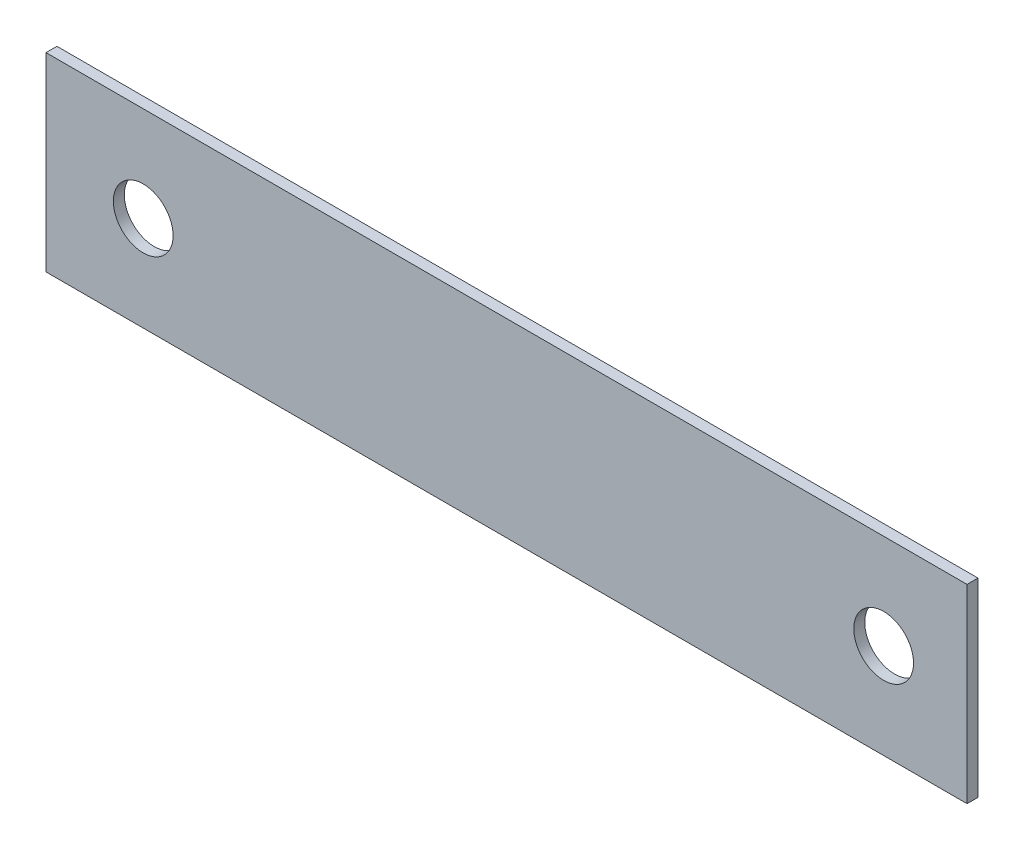
SolidWorks part; units mm, degrees
ref_plane "Front Plane" through (0, 0, 0) normal (0, 0, 1) x (1, 0, 0)
ref_plane "Top Plane" through (0, 0, 0) normal (0, 1, 0) x (1, 0, 0)
ref_plane "Right Plane" through (0, 0, 0) normal (1, 0, 0) x (0, 0, -1)
sketch "Sketch1" plane through (0, 0, 0) normal (0, 0, 1) x (1, 0, 0)
  line L1 (-18.5, -3.815) -> (18.5, -3.815)
  line L2 (-18.5, -3.815) -> (-18.5, 3.815)
  line L3 (-18.5, 3.815) -> (18.5, 3.815)
  line L4 (18.5, -3.815) -> (18.5, 3.815)
  line L5 (-18.5, -3.815) -> (18.5, 3.815) construction
  line L6 (-18.5, 3.815) -> (18.5, -3.815) construction
  circle A0 centre (-14.5941, 0) radius 1.2
  circle A1 centre (15.15, 0) radius 1.2
  point P0 (0, 0)
  point P10 (0, 0)
  point P11 (0, 0)
  dimension "D3" = 2.4
  dimension "D4" = 2.4
  dimension "D1" = 37
  dimension "D2" = 7.63
  dimension "D5" = 3.35
  dimension "D6" = 3.9059
extrude "Boss-Extrude1" add sketch "Sketch1" along normal blind 0.44
ref_plane "Plane1" through (-5.295, 0, 0) normal (1, 0, 0) x (0, 0, -1)
sketch "Sketch3" plane through (-5.295, 0, 0) normal (1, 0, 0) x (0, 0, -1)
  line L0 (2.2275, 0.8907) -> (0, 2.71)
  line L2 (2.2275, -0.8907) -> (0, -2.71)
  line L3 (0, 2.71) -> (0, -2.71)
  arc A0 (2.2275, -0.8907) -> (2.2275, 0.8907) centre (1.5, 0) ccw
  circle A1 centre (1.5, 0) radius 1.05
  point P6 (0, 0)
  point P7 (1.5555, 0)
  point P10 (1.3723, 1.15)
  point P11 (1.0898, -1.6004)
  point P12 (1.4792, 0)
  point P13 (0, 0)
  point P14 (2.196, 0.9154)
  point P15 (2.1244, -0.9657)
  dimension "D1" = 2.3
  dimension "D2" = 2.1
  dimension "D3" = 5.42
  dimension "D4" = 1.5
sketch "Sketch4" plane through (0, 0, 0) normal (0, 1, 0) x (1, 0, 0)
  line L0 (-5.295, 1.5) -> (-5.295, 0) construction
  line L1 (18.5, 0) -> (-18.5, 0) construction
  arc A0 (-5.295, 1.5) -> (-7.6188, 0) centre (-5.295, -1.05) ccw
  point P4 (-7.6176, 0)
  dimension "D1" = 2.55
extrude "Boss-Extrude2" add sketch "Sketch3" against normal blind 4.85
mirror "Mirror1" about plane through (0, 0, 0) normal (1, 0, 0) of "Boss-Extrude2"
